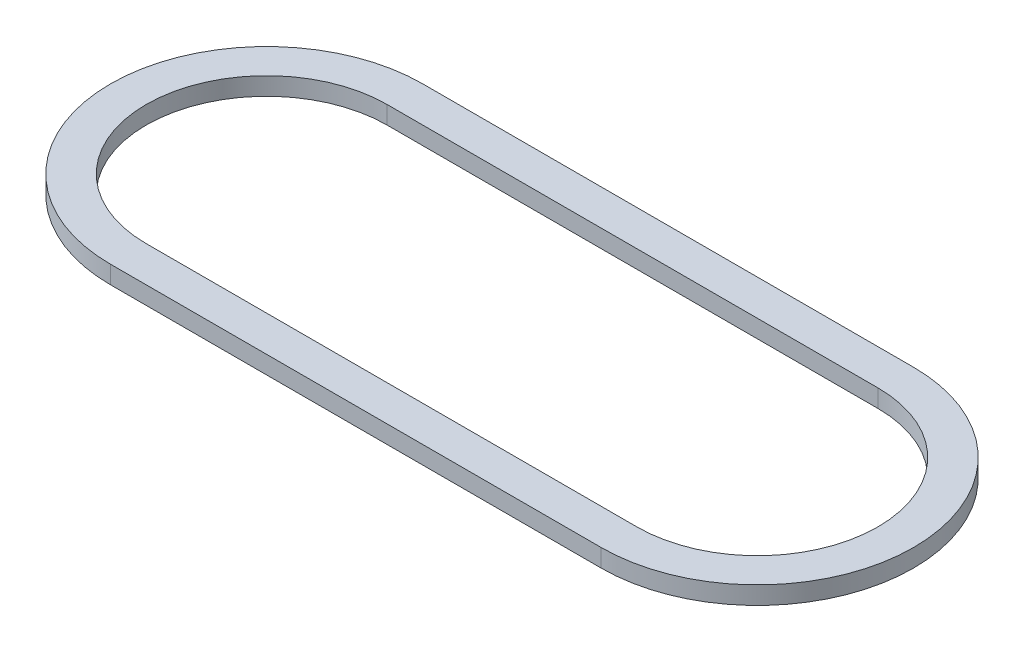
SolidWorks part; units mm, degrees
material "NBR"
ref_plane "Front Plane" through (0, 0, 0) normal (0, 0, 1) x (1, 0, 0)
ref_plane "Top Plane" through (0, 0, 0) normal (0, 1, 0) x (1, 0, 0)
ref_plane "Right Plane" through (0, 0, 0) normal (1, 0, 0) x (0, 0, -1)
sketch "Sketch1" plane through (0, 0, 0) normal (0, 1, 0) x (1, 0, 0)
  line L0 (-6.985, 0) -> (6.985, 0) construction
  line L1 (-6.985, 3.429) -> (6.985, 3.429)
  line L2 (-6.985, -3.429) -> (6.985, -3.429)
  line L3 (-6.985, 0) -> (6.985, 0) construction
  line L4 (-6.985, 4.445) -> (6.985, 4.445)
  line L5 (-6.985, -4.445) -> (6.985, -4.445)
  arc A0 (-6.985, 3.429) -> (-6.985, -3.429) centre (-6.985, 0) ccw
  arc A1 (6.985, -3.429) -> (6.985, 3.429) centre (6.985, 0) ccw
  arc A2 (-6.985, 4.445) -> (-6.985, -4.445) centre (-6.985, 0) ccw
  arc A3 (6.985, -4.445) -> (6.985, 4.445) centre (6.985, 0) ccw
  point P2 (0, 0)
  point P9 (0, 0)
  dimension "D2" = 4.445
  dimension "D1" = 1.016
  dimension "D3" = 13.97
extrude "Boss-Extrude1" add sketch "Sketch1" along normal blind 0.508
equation "\"w\"= 0.04"
equation "\"D2@Sketch1\"= .185 - .01 '10 thou smaller than channel rad"
equation "\"D1@Sketch1\"=\"w\""
